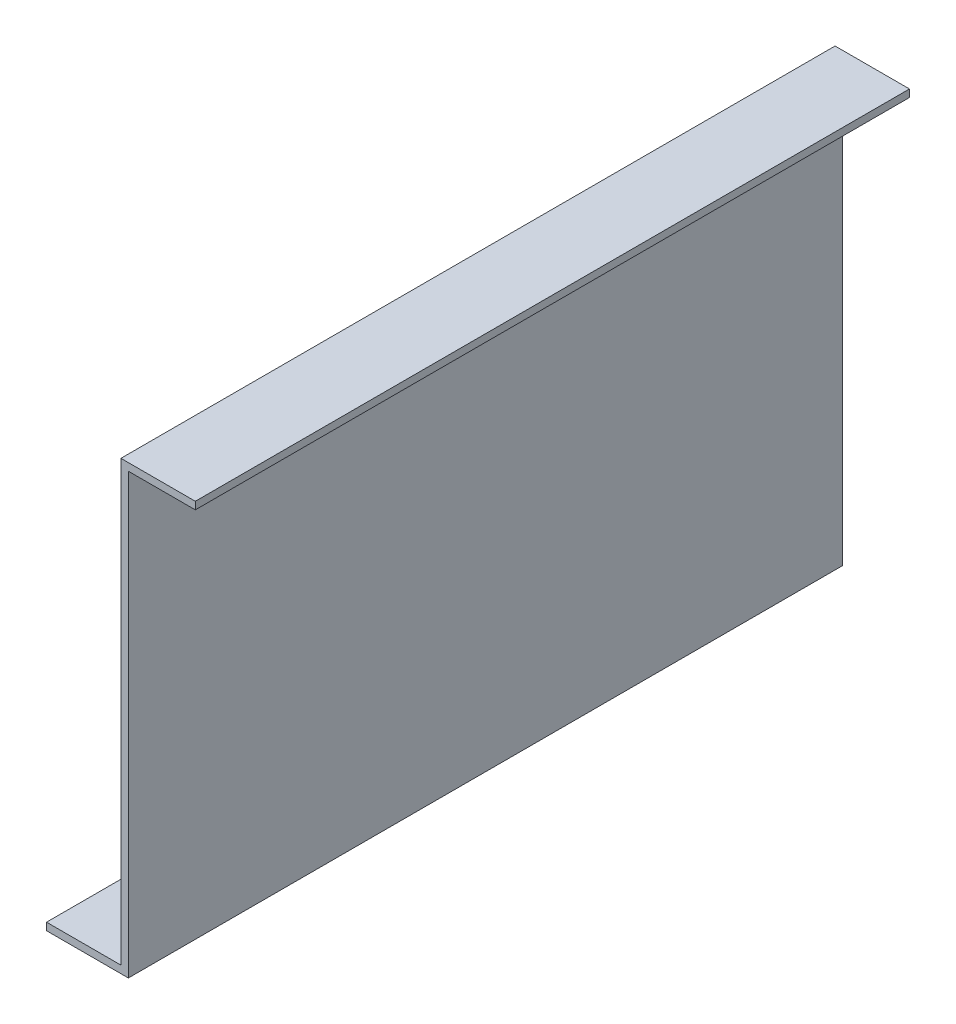
SolidWorks part; units mm, degrees
ref_plane "Plan de face" through (0, 0, 0) normal (0, 0, 1) x (1, 0, 0)
ref_plane "Plan de dessus" through (0, 0, 0) normal (0, 1, 0) x (1, 0, 0)
ref_plane "Plan de droite" through (0, 0, 0) normal (1, 0, 0) x (0, 0, -1)
sketch "Esquisse1" plane through (0, 0, 0) normal (0, 0, 1) x (1, 0, 0)
  line L0 (0, 0) -> (20, 0)
  line L1 (20, 0) -> (20, 118)
  line L2 (20, 118) -> (40, 118)
  dimension "D1" = 20
  dimension "D2" = 118
extrude "Extru.-Mince1" add sketch "Esquisse1" along normal blind 192 thin
